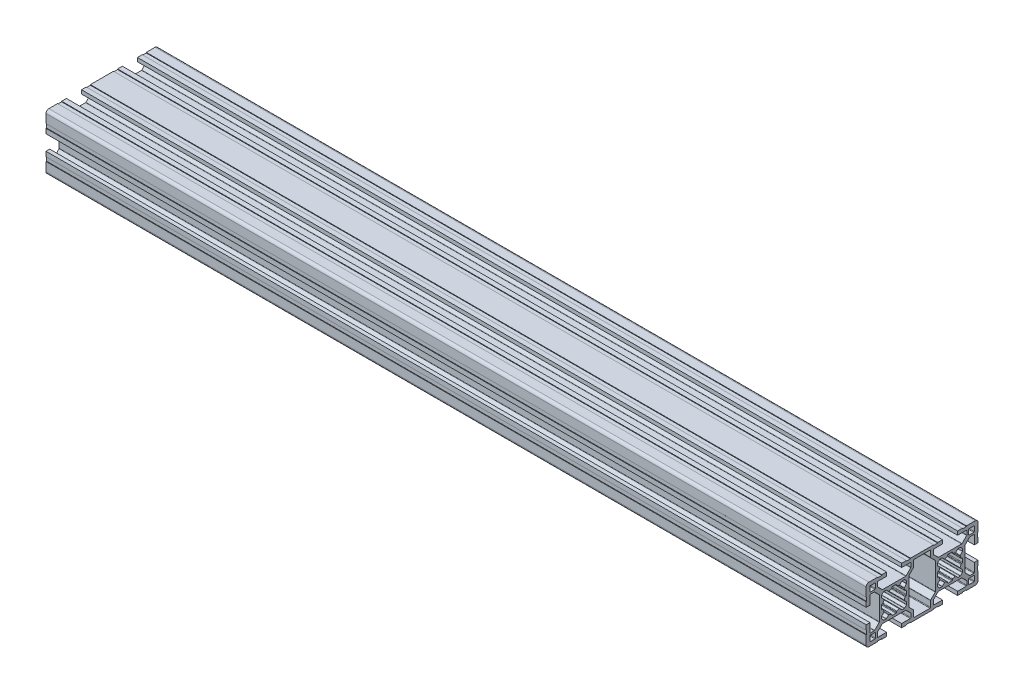
SolidWorks part; units mm, degrees
material "6063-T5 (Padrão)"
ref_plane "Plano frontal" through (0, 0, 0) normal (0, 0, 1) x (1, 0, 0)
ref_plane "Plano superior" through (0, 0, 0) normal (0, 1, 0) x (1, 0, 0)
ref_plane "Plano direito" through (0, 0, 0) normal (1, 0, 0) x (0, 0, -1)
sketch "Esboço1" plane through (0, 0, 0) normal (0, 0, 1) x (1, 0, 0)
  line L0 (-220, 0) -> (220, 0)
  point P4 (0, 0)
  dimension "D1" = 440
other "Retangular PF30-02 - PERFIL 3060 BÁSICO(1)"
ref_plane "Plano1" through (-220, 0, 0) normal (1, 0, 0) x (0, 1, 0)
sketch "Sketch11" plane through (-220, 0, 0) normal (1, 0, 0) x (0, 1, 0)
  line L0 (-9.8464, -4.5906) -> (-7.4222, -7.0149)
  line L1 (-7.21, -7.1028) -> (7.21, -7.1028)
  line L2 (7.4222, -7.0149) -> (9.8464, -4.5906)
  line L3 (10.0586, -4.5028) -> (13.2, -4.5028)
  line L4 (13.5, -4.2028) -> (13.5, 4.1972)
  line L5 (13.2, 4.4972) -> (10.0586, 4.4972)
  line L6 (9.8464, 4.5851) -> (7.4222, 7.0094)
  line L7 (7.21, 7.0972) -> (-7.21, 7.0972)
  line L8 (-7.4222, 7.0094) -> (-9.8464, 4.5851)
  line L9 (-10.0586, 4.4972) -> (-13.2, 4.4972)
  line L10 (-13.5, 4.1972) -> (-13.5, -4.2028)
  line L11 (-13.2, -4.5028) -> (-10.0586, -4.5028)
  line L12 (-6.7, 15.9528) -> (-6.7, 14.0528)
  line L13 (-6.1579, 16.2528) -> (-6.4, 16.2528)
  line L14 (-6.6121, 19.14) -> (-5.4871, 18.015)
  line L15 (-6.7, 20.4423) -> (-6.7, 19.3522)
  line L16 (-6.1319, 21.1347) -> (-6.6121, 20.6545)
  line L17 (-10.4678, 23.9149) -> (-7.9879, 21.435)
  line L18 (-12.7, 24.0028) -> (-10.6799, 24.0028)
  line L19 (-13, 19.0528) -> (-13, 23.7028)
  line L20 (-13, 19.0528) -> (-15, 19.0528)
  line L21 (6.7, 15.9528) -> (6.7, 14.0528)
  line L22 (7.9, 21.2229) -> (7.9, 8.7827)
  line L23 (15, 21.6028) -> (15, 19.0528)
  line L24 (-5.4396, 21.7028) -> (-4.3494, 21.7028)
  line L25 (-13, 25.3028) -> (-13, 27.7028)
  line L26 (-4.05, 28.0028) -> (-8.7, 28.0028)
  line L27 (-12.7, 28.0028) -> (-10.3, 28.0028)
  line L28 (-9, 27.7028) -> (-9, 25.6827)
  line L29 (-10, 27.7028) -> (-10, 25.3028)
  line L30 (-8.9121, 25.4705) -> (-6.4322, 22.9906)
  line L31 (15, 23.8028) -> (14.7, 23.8028)
  line L32 (14.7, 23.8028) -> (14.7, 21.6028)
  line L33 (15, 28.5028) -> (15, 23.8028)
  line L34 (8.8, 30.0028) -> (13.5, 30.0028)
  line L35 (8.8, 29.7028) -> (6.6, 29.7028)
  line L36 (4.05, 30.0028) -> (6.6, 30.0028)
  line L37 (4.05, 28.0028) -> (4.05, 30.0028)
  line L38 (10.3, 25.0028) -> (12.7, 25.0028)
  line L39 (15, 21.6028) -> (14.7, 21.6028)
  line L40 (6.6, 30.0028) -> (6.6, 29.7028)
  line L41 (-6.1319, 21.1347) -> (-5.6517, 21.6149)
  line L42 (-4.1373, 21.6149) -> (-3.0123, 20.4899)
  line L43 (-1.25, 21.1607) -> (-1.25, 21.4028)
  line L44 (8.8, 30.0028) -> (8.8, 29.7028)
  line L45 (1.25, 21.1607) -> (1.25, 21.4028)
  line L46 (4.1373, 21.6149) -> (3.0123, 20.4899)
  line L47 (6.1319, 21.1347) -> (5.6517, 21.6149)
  line L48 (8.9121, 25.4705) -> (6.4322, 22.9906)
  line L49 (10, 27.7028) -> (10, 25.3028)
  line L50 (9, 27.7028) -> (9, 25.6827)
  line L51 (12.7, 28.0028) -> (10.3, 28.0028)
  line L52 (4.05, 28.0028) -> (8.7, 28.0028)
  line L53 (13, 25.3028) -> (13, 27.7028)
  line L54 (5.4396, 21.7028) -> (4.3494, 21.7028)
  line L55 (13, 19.0528) -> (15, 19.0528)
  line L56 (13, 19.0528) -> (13, 23.7028)
  line L57 (12.7, 24.0028) -> (10.6799, 24.0028)
  line L58 (10.4678, 23.9149) -> (7.9879, 21.435)
  line L59 (6.1319, 21.1347) -> (6.6121, 20.6545)
  line L60 (6.7, 20.4423) -> (6.7, 19.3522)
  line L61 (6.6121, 19.14) -> (5.4871, 18.015)
  line L62 (6.1579, 16.2528) -> (6.4, 16.2528)
  line L63 (-7.9, 8.7827) -> (-7.9, 21.2229)
  line L64 (-0.95, 8.3028) -> (0.95, 8.3028)
  line L65 (-15, 8.4028) -> (-15, 10.9528)
  line L66 (-15, 6.2028) -> (-14.7, 6.2028)
  line L67 (-14.7, 6.2028) -> (-14.7, 8.4028)
  line L68 (-15, -14.9972) -> (15, -14.9972) construction
  line L69 (-6.1579, -13.7472) -> (-6.4, -13.7472)
  line L70 (-6.6121, -10.86) -> (-5.4871, -11.985)
  line L71 (-6.7, -9.5577) -> (-6.7, -10.6478)
  line L72 (-15, 8.4028) -> (-14.7, 8.4028)
  line L73 (-0.95, -21.6972) -> (0.95, -21.6972)
  line L74 (-6.1319, -8.8653) -> (-6.6121, -9.3455)
  line L75 (6.1579, 13.7528) -> (6.4, 13.7528)
  line L76 (6.6121, 10.8655) -> (5.4871, 11.9905)
  line L77 (6.7, 9.5632) -> (6.7, 10.6534)
  line L78 (6.1319, 8.8709) -> (6.6121, 9.3511)
  line L79 (10.4678, 6.0906) -> (7.9879, 8.5705)
  line L80 (12.7, 6.0028) -> (10.6799, 6.0028)
  line L81 (13, 10.9528) -> (13, 6.3028)
  line L82 (13, 10.9528) -> (15, 10.9528)
  line L83 (5.4396, 8.3028) -> (4.3494, 8.3028)
  line L84 (-10.4678, -6.0851) -> (-7.9879, -8.565)
  line L85 (-8.8, 30.0028) -> (-8.8, 29.7028)
  line L86 (-12.7, -5.9972) -> (-10.6799, -5.9972)
  line L87 (-13, -10.9472) -> (-13, -6.2972)
  line L88 (-13, -10.9472) -> (-15, -10.9472)
  line L89 (15, -8.3972) -> (15, -10.9472)
  line L90 (-5.4396, -8.2972) -> (-4.3494, -8.2972)
  line L91 (6.1319, 8.8709) -> (5.6517, 8.3906)
  line L92 (4.1373, 8.3906) -> (3.0123, 9.5156)
  line L93 (1.25, 8.8448) -> (1.25, 8.6028)
  line L94 (-15, -21.5972) -> (-15, -19.0472)
  line L95 (-6.6, 30.0028) -> (-6.6, 29.7028)
  line L96 (-1.25, 8.8448) -> (-1.25, 8.6028)
  line L97 (-4.1373, 8.3906) -> (-3.0123, 9.5156)
  line L98 (-6.1319, 8.8709) -> (-5.6517, 8.3906)
  line L99 (-15, -23.7972) -> (-14.7, -23.7972)
  line L100 (15, 8.4028) -> (14.7, 8.4028)
  line L101 (-14.7, -23.7972) -> (-14.7, -21.5972)
  line L102 (-15, -28.4972) -> (-15, -23.7972)
  line L103 (-8.8, -29.9972) -> (-13.5, -29.9972)
  line L104 (-8.8, -29.6972) -> (-6.6, -29.6972)
  line L105 (-4.05, -29.9972) -> (-6.6, -29.9972)
  line L106 (14.7, 6.2028) -> (14.7, 8.4028)
  line L107 (15, 6.2028) -> (14.7, 6.2028)
  line L108 (-4.05, -27.9972) -> (-4.05, -29.9972)
  line L109 (-10.3, -24.9972) -> (-12.7, -24.9972)
  line L110 (-6.2201, -22.8972) -> (6.2201, -22.8972)
  line L111 (-15, -21.5972) -> (-14.7, -21.5972)
  line L112 (15, -6.1972) -> (14.7, -6.1972)
  line L113 (-15, 21.6028) -> (-14.7, 21.6028)
  line L114 (-6.2201, 22.9028) -> (6.2201, 22.9028)
  line L115 (-10.3, 25.0028) -> (-12.7, 25.0028)
  line L116 (-4.05, 28.0028) -> (-4.05, 30.0028)
  line L117 (-4.05, 30.0028) -> (-6.6, 30.0028)
  line L118 (-8.8, 29.7028) -> (-6.6, 29.7028)
  line L119 (0, 29.9972) -> (0, -29.9972) construction
  line L120 (-15, 15.0028) -> (15, 15.0028) construction
  line L121 (-8.8, 30.0028) -> (-13.5, 30.0028)
  line L122 (-15, 28.5028) -> (-15, 23.8028)
  line L123 (-14.7, 23.8028) -> (-14.7, 21.6028)
  line L124 (-15, 23.8028) -> (-14.7, 23.8028)
  line L125 (-15, 21.6028) -> (-15, 19.0528)
  line L126 (14.7, -6.1972) -> (14.7, -8.3972)
  line L127 (-5.4396, 8.3028) -> (-4.3494, 8.3028)
  line L128 (15, 8.4028) -> (15, 10.9528)
  line L129 (15, 6.2028) -> (15, -6.1972)
  line L130 (-13, 10.9528) -> (-15, 10.9528)
  line L131 (-13, 10.9528) -> (-13, 6.3028)
  line L132 (-12.7, 6.0028) -> (-10.6799, 6.0028)
  line L133 (-10.4678, 6.0906) -> (-7.9879, 8.5705)
  line L134 (-6.1319, 8.8709) -> (-6.6121, 9.3511)
  line L135 (-0.95, 21.7028) -> (0.95, 21.7028)
  line L136 (-6.7, 9.5632) -> (-6.7, 10.6534)
  line L137 (-6.6121, 10.8655) -> (-5.4871, 11.9905)
  line L138 (-6.1579, 13.7528) -> (-6.4, 13.7528)
  line L139 (15, 0.0028) -> (-15, 0.0028) construction
  line L140 (15, -8.3972) -> (14.7, -8.3972)
  line L141 (-6.1319, -8.8653) -> (-5.6517, -8.3851)
  line L142 (-4.1373, -8.3851) -> (-3.0123, -9.5101)
  line L143 (-1.25, -8.8393) -> (-1.25, -8.5972)
  line L144 (-6.6, -29.9972) -> (-6.6, -29.6972)
  line L145 (1.25, -8.8393) -> (1.25, -8.5972)
  line L146 (4.1373, -8.3851) -> (3.0123, -9.5101)
  line L147 (6.1319, -8.8653) -> (5.6517, -8.3851)
  line L148 (-8.8, -29.9972) -> (-8.8, -29.6972)
  line L149 (5.4396, -8.2972) -> (4.3494, -8.2972)
  line L150 (13, -10.9472) -> (15, -10.9472)
  line L151 (13, -10.9472) -> (13, -6.2972)
  line L152 (12.7, -5.9972) -> (10.6799, -5.9972)
  line L153 (10.4678, -6.0851) -> (7.9879, -8.565)
  line L154 (6.1319, -8.8653) -> (6.6121, -9.3455)
  line L155 (6.7, -9.5577) -> (6.7, -10.6478)
  line L156 (6.6121, -10.86) -> (5.4871, -11.985)
  line L157 (6.1579, -13.7472) -> (6.4, -13.7472)
  line L158 (-15, -8.3972) -> (-14.7, -8.3972)
  line L159 (-15, 6.2028) -> (-15, -6.1972)
  line L160 (-14.7, -6.1972) -> (-14.7, -8.3972)
  line L161 (-15, -6.1972) -> (-14.7, -6.1972)
  line L162 (-15, -8.3972) -> (-15, -10.9472)
  line L163 (-0.95, -8.2972) -> (0.95, -8.2972)
  line L164 (-7.9, -8.7771) -> (-7.9, -21.2173)
  line L165 (6.1579, -16.2472) -> (6.4, -16.2472)
  line L166 (6.6121, -19.1345) -> (5.4871, -18.0095)
  line L167 (6.7, -20.4368) -> (6.7, -19.3466)
  line L168 (6.1319, -21.1291) -> (6.6121, -20.6489)
  line L169 (10.4678, -23.9094) -> (7.9879, -21.4295)
  line L170 (12.7, -23.9972) -> (10.6799, -23.9972)
  line L171 (13, -19.0472) -> (13, -23.6972)
  line L172 (13, -19.0472) -> (15, -19.0472)
  line L173 (5.4396, -21.6972) -> (4.3494, -21.6972)
  line L174 (13, -25.2972) -> (13, -27.6972)
  line L175 (4.05, -27.9972) -> (8.7, -27.9972)
  line L176 (12.7, -27.9972) -> (10.3, -27.9972)
  line L177 (9, -27.6972) -> (9, -25.6771)
  line L178 (10, -27.6972) -> (10, -25.2972)
  line L179 (8.9121, -25.465) -> (6.4322, -22.9851)
  line L180 (6.1319, -21.1291) -> (5.6517, -21.6093)
  line L181 (4.1373, -21.6093) -> (3.0123, -20.4844)
  line L182 (1.25, -21.1551) -> (1.25, -21.3972)
  line L183 (8.8, -29.9972) -> (8.8, -29.6972)
  line L184 (-1.25, -21.1551) -> (-1.25, -21.3972)
  line L185 (-4.1373, -21.6093) -> (-3.0123, -20.4844)
  line L186 (-6.1319, -21.1291) -> (-5.6517, -21.6093)
  line L187 (6.6, -29.9972) -> (6.6, -29.6972)
  line L188 (15, -21.5972) -> (14.7, -21.5972)
  line L189 (10.3, -24.9972) -> (12.7, -24.9972)
  line L190 (4.05, -27.9972) -> (4.05, -29.9972)
  line L191 (4.05, -29.9972) -> (6.6, -29.9972)
  line L192 (8.8, -29.6972) -> (6.6, -29.6972)
  line L193 (8.8, -29.9972) -> (13.5, -29.9972)
  line L194 (15, -28.4972) -> (15, -23.7972)
  line L195 (14.7, -23.7972) -> (14.7, -21.5972)
  line L196 (15, -23.7972) -> (14.7, -23.7972)
  line L197 (-8.9121, -25.465) -> (-6.4322, -22.9851)
  line L198 (-10, -27.6972) -> (-10, -25.2972)
  line L199 (-9, -27.6972) -> (-9, -25.6771)
  line L200 (-12.7, -27.9972) -> (-10.3, -27.9972)
  line L201 (-4.05, -27.9972) -> (-8.7, -27.9972)
  line L202 (-13, -25.2972) -> (-13, -27.6972)
  line L203 (-5.4396, -21.6972) -> (-4.3494, -21.6972)
  line L204 (15, -21.5972) -> (15, -19.0472)
  line L205 (7.9, -21.2173) -> (7.9, -8.7771)
  line L206 (6.7, -15.9472) -> (6.7, -14.0472)
  line L207 (-13, -19.0472) -> (-15, -19.0472)
  line L208 (-13, -19.0472) -> (-13, -23.6972)
  line L209 (-12.7, -23.9972) -> (-10.6799, -23.9972)
  line L210 (-10.4678, -23.9094) -> (-7.9879, -21.4295)
  line L211 (-6.1319, -21.1291) -> (-6.6121, -20.6489)
  line L212 (-6.7, -20.4368) -> (-6.7, -19.3466)
  line L213 (-6.6121, -19.1345) -> (-5.4871, -18.0095)
  line L214 (-6.1579, -16.2472) -> (-6.4, -16.2472)
  line L215 (-6.7, -15.9472) -> (-6.7, -14.0472)
  arc A0 (-9.8464, -4.5906) -> (-10.0586, -4.5028) centre (-10.0586, -4.8028) ccw
  arc A1 (-7.4222, -7.0149) -> (-7.21, -7.1028) centre (-7.21, -6.8028) ccw
  arc A2 (7.21, -7.1028) -> (7.4222, -7.0149) centre (7.21, -6.8028) ccw
  arc A3 (10.0586, -4.5028) -> (9.8464, -4.5906) centre (10.0586, -4.8028) ccw
  arc A4 (13.2, -4.5028) -> (13.5, -4.2028) centre (13.2, -4.2028) ccw
  arc A5 (13.5, 4.1972) -> (13.2, 4.4972) centre (13.2, 4.1972) ccw
  arc A6 (9.8464, 4.5851) -> (10.0586, 4.4972) centre (10.0586, 4.7972) ccw
  arc A7 (7.4222, 7.0094) -> (7.21, 7.0972) centre (7.21, 6.7972) ccw
  arc A8 (-7.21, 7.0972) -> (-7.4222, 7.0094) centre (-7.21, 6.7972) ccw
  arc A9 (-10.0586, 4.4972) -> (-9.8464, 4.5851) centre (-10.0586, 4.7972) ccw
  arc A10 (-13.2, 4.4972) -> (-13.5, 4.1972) centre (-13.2, 4.1972) ccw
  arc A11 (-13.5, -4.2028) -> (-13.2, -4.5028) centre (-13.2, -4.2028) ccw
  arc A12 (-6.4, 16.2528) -> (-6.7, 15.9528) centre (-6.4, 15.9528) ccw
  arc A13 (-5.867, 16.4795) -> (-6.1579, 16.2528) centre (-6.1579, 16.5528) cw
  arc A14 (-5.867, 16.4795) -> (-5.43, 17.6706) centre (0, 15.0028) cw
  arc A15 (-5.4871, 18.015) -> (-5.43, 17.6706) centre (-5.6993, 17.8029) cw
  arc A16 (-6.6121, 19.14) -> (-6.7, 19.3522) centre (-6.4, 19.3522) cw
  arc A17 (-6.6121, 20.6545) -> (-6.7, 20.4423) centre (-6.4, 20.4423) ccw
  arc A18 (-7.9879, 21.435) -> (-7.9, 21.2229) centre (-8.2, 21.2229) cw
  arc A19 (-10.6799, 24.0028) -> (-10.4678, 23.9149) centre (-10.6799, 23.7028) cw
  arc A20 (-13, 23.7028) -> (-12.7, 24.0028) centre (-12.7, 23.7028) cw
  arc A21 (13.5, 30.0028) -> (15, 28.5028) centre (13.5, 28.5028) cw
  arc A22 (1.25, 21.4028) -> (0.95, 21.7028) centre (0.95, 21.4028) ccw
  arc A23 (4.1373, 21.6149) -> (4.3494, 21.7028) centre (4.3494, 21.4028) cw
  arc A24 (1.4768, 20.8698) -> (1.25, 21.1607) centre (1.55, 21.1607) cw
  arc A25 (1.4768, 20.8698) -> (2.6678, 20.4328) centre (0, 15.0028) cw
  arc A26 (-10.3, 25.0028) -> (-10, 25.3028) centre (-10.3, 25.3028) ccw
  arc A27 (-6.4322, 22.9906) -> (-6.2201, 22.9028) centre (-6.2201, 23.2028) ccw
  arc A28 (-13, 25.3028) -> (-12.7, 25.0028) centre (-12.7, 25.3028) ccw
  arc A29 (-9, 25.6827) -> (-8.9121, 25.4705) centre (-8.7, 25.6827) ccw
  arc A30 (-10, 27.7028) -> (-10.3, 28.0028) centre (-10.3, 27.7028) ccw
  arc A31 (-8.7, 28.0028) -> (-9, 27.7028) centre (-8.7, 27.7028) ccw
  arc A32 (-12.7, 28.0028) -> (-13, 27.7028) centre (-12.7, 27.7028) ccw
  arc A33 (3.0123, 20.4899) -> (2.6678, 20.4328) centre (2.8001, 20.702) cw
  arc A34 (5.6517, 21.6149) -> (5.4396, 21.7028) centre (5.4396, 21.4028) ccw
  arc A35 (12.7, 28.0028) -> (13, 27.7028) centre (12.7, 27.7028) cw
  arc A36 (8.7, 28.0028) -> (9, 27.7028) centre (8.7, 27.7028) cw
  arc A37 (10, 27.7028) -> (10.3, 28.0028) centre (10.3, 27.7028) cw
  arc A38 (9, 25.6827) -> (8.9121, 25.4705) centre (8.7, 25.6827) cw
  arc A39 (13, 25.3028) -> (12.7, 25.0028) centre (12.7, 25.3028) cw
  arc A40 (6.4322, 22.9906) -> (6.2201, 22.9028) centre (6.2201, 23.2028) cw
  arc A41 (10.3, 25.0028) -> (10, 25.3028) centre (10.3, 25.3028) cw
  arc A42 (13, 23.7028) -> (12.7, 24.0028) centre (12.7, 23.7028) ccw
  arc A43 (10.6799, 24.0028) -> (10.4678, 23.9149) centre (10.6799, 23.7028) ccw
  arc A44 (7.9879, 21.435) -> (7.9, 21.2229) centre (8.2, 21.2229) ccw
  arc A45 (6.6121, 20.6545) -> (6.7, 20.4423) centre (6.4, 20.4423) cw
  arc A46 (6.6121, 19.14) -> (6.7, 19.3522) centre (6.4, 19.3522) ccw
  arc A47 (5.4871, 18.015) -> (5.43, 17.6706) centre (5.6993, 17.8029) ccw
  arc A48 (5.867, 16.4795) -> (5.43, 17.6706) centre (0, 15.0028) ccw
  arc A49 (5.867, 16.4795) -> (6.1579, 16.2528) centre (6.1579, 16.5528) ccw
  arc A50 (6.4, 16.2528) -> (6.7, 15.9528) centre (6.4, 15.9528) cw
  arc A51 (6.4, 13.7528) -> (6.7, 14.0528) centre (6.4, 14.0528) ccw
  arc A52 (-5.6517, 21.6149) -> (-5.4396, 21.7028) centre (-5.4396, 21.4028) cw
  arc A53 (-3.0123, 20.4899) -> (-2.6678, 20.4328) centre (-2.8001, 20.702) ccw
  arc A54 (-1.4768, 20.8698) -> (-2.6678, 20.4328) centre (0, 15.0028) ccw
  arc A55 (-1.4768, 20.8698) -> (-1.25, 21.1607) centre (-1.55, 21.1607) ccw
  arc A56 (-4.1373, 21.6149) -> (-4.3494, 21.7028) centre (-4.3494, 21.4028) ccw
  arc A57 (-6.4, 13.7528) -> (-6.7, 14.0528) centre (-6.4, 14.0528) cw
  arc A58 (-13.5, -29.9972) -> (-15, -28.4972) centre (-13.5, -28.4972) cw
  arc A59 (-1.25, 8.6028) -> (-0.95, 8.3028) centre (-0.95, 8.6028) ccw
  arc A60 (-4.1373, 8.3906) -> (-4.3494, 8.3028) centre (-4.3494, 8.6028) cw
  arc A61 (-1.4768, 9.1358) -> (-1.25, 8.8448) centre (-1.55, 8.8448) cw
  arc A62 (-1.4768, 9.1358) -> (-2.6678, 9.5728) centre (0, 15.0028) cw
  arc A63 (-3.0123, 9.5156) -> (-2.6678, 9.5728) centre (-2.8001, 9.3035) cw
  arc A64 (-5.6517, 8.3906) -> (-5.4396, 8.3028) centre (-5.4396, 8.6028) ccw
  arc A65 (5.867, 13.526) -> (6.1579, 13.7528) centre (6.1579, 13.4528) cw
  arc A66 (5.867, 13.526) -> (5.43, 12.3349) centre (0, 15.0028) cw
  arc A67 (5.4871, 11.9905) -> (5.43, 12.3349) centre (5.6993, 12.2026) cw
  arc A68 (6.6121, 10.8655) -> (6.7, 10.6534) centre (6.4, 10.6534) cw
  arc A69 (6.6121, 9.3511) -> (6.7, 9.5632) centre (6.4, 9.5632) ccw
  arc A70 (7.9879, 8.5705) -> (7.9, 8.7827) centre (8.2, 8.7827) cw
  arc A71 (10.6799, 6.0028) -> (10.4678, 6.0906) centre (10.6799, 6.3028) cw
  arc A72 (13, 6.3028) -> (12.7, 6.0028) centre (12.7, 6.3028) cw
  arc A73 (-5.867, -13.5205) -> (-6.1579, -13.7472) centre (-6.1579, -13.4472) cw
  arc A74 (-5.867, -13.5205) -> (-5.43, -12.3294) centre (0, -14.9972) cw
  arc A75 (-1.25, -21.3972) -> (-0.95, -21.6972) centre (-0.95, -21.3972) ccw
  arc A76 (-5.4871, -11.985) -> (-5.43, -12.3294) centre (-5.6993, -12.1971) cw
  arc A77 (-6.6121, -10.86) -> (-6.7, -10.6478) centre (-6.4, -10.6478) cw
  arc A78 (-6.6121, -9.3455) -> (-6.7, -9.5577) centre (-6.4, -9.5577) ccw
  arc A79 (-7.9879, -8.565) -> (-7.9, -8.7771) centre (-8.2, -8.7771) cw
  arc A80 (5.6517, 8.3906) -> (5.4396, 8.3028) centre (5.4396, 8.6028) cw
  arc A81 (3.0123, 9.5156) -> (2.6678, 9.5728) centre (2.8001, 9.3035) ccw
  arc A82 (-10.6799, -5.9972) -> (-10.4678, -6.0851) centre (-10.6799, -6.2972) cw
  arc A83 (-13, -6.2972) -> (-12.7, -5.9972) centre (-12.7, -6.2972) cw
  arc A84 (1.25, -8.5972) -> (0.95, -8.2972) centre (0.95, -8.5972) ccw
  arc A85 (4.1373, -8.3851) -> (4.3494, -8.2972) centre (4.3494, -8.5972) cw
  arc A86 (1.4768, -9.1302) -> (1.25, -8.8393) centre (1.55, -8.8393) cw
  arc A87 (1.4768, -9.1302) -> (2.6678, -9.5672) centre (0, -14.9972) cw
  arc A88 (3.0123, -9.5101) -> (2.6678, -9.5672) centre (2.8001, -9.2979) cw
  arc A89 (1.4768, 9.1358) -> (2.6678, 9.5728) centre (0, 15.0028) ccw
  arc A90 (1.4768, 9.1358) -> (1.25, 8.8448) centre (1.55, 8.8448) ccw
  arc A91 (4.1373, 8.3906) -> (4.3494, 8.3028) centre (4.3494, 8.6028) ccw
  arc A92 (1.25, 8.6028) -> (0.95, 8.3028) centre (0.95, 8.6028) cw
  arc A93 (5.6517, -8.3851) -> (5.4396, -8.2972) centre (5.4396, -8.5972) ccw
  arc A94 (-13, 6.3028) -> (-12.7, 6.0028) centre (-12.7, 6.3028) ccw
  arc A95 (-10.6799, 6.0028) -> (-10.4678, 6.0906) centre (-10.6799, 6.3028) ccw
  arc A96 (-7.9879, 8.5705) -> (-7.9, 8.7827) centre (-8.2, 8.7827) ccw
  arc A97 (-6.6121, 9.3511) -> (-6.7, 9.5632) centre (-6.4, 9.5632) cw
  arc A98 (-6.6121, 10.8655) -> (-6.7, 10.6534) centre (-6.4, 10.6534) ccw
  arc A99 (-5.4871, 11.9905) -> (-5.43, 12.3349) centre (-5.6993, 12.2026) ccw
  arc A100 (-1.25, 21.4028) -> (-0.95, 21.7028) centre (-0.95, 21.4028) cw
  arc A101 (-5.867, 13.526) -> (-5.43, 12.3349) centre (0, 15.0028) ccw
  arc A102 (-5.867, 13.526) -> (-6.1579, 13.7528) centre (-6.1579, 13.4528) ccw
  arc A103 (-13.5, 30.0028) -> (-15, 28.5028) centre (-13.5, 28.5028) ccw
  arc A104 (13, -6.2972) -> (12.7, -5.9972) centre (12.7, -6.2972) ccw
  arc A105 (10.6799, -5.9972) -> (10.4678, -6.0851) centre (10.6799, -6.2972) ccw
  arc A106 (7.9879, -8.565) -> (7.9, -8.7771) centre (8.2, -8.7771) ccw
  arc A107 (6.6121, -9.3455) -> (6.7, -9.5577) centre (6.4, -9.5577) cw
  arc A108 (6.6121, -10.86) -> (6.7, -10.6478) centre (6.4, -10.6478) ccw
  arc A109 (5.4871, -11.985) -> (5.43, -12.3294) centre (5.6993, -12.1971) ccw
  arc A110 (5.867, -13.5205) -> (5.43, -12.3294) centre (0, -14.9972) ccw
  arc A111 (5.867, -13.5205) -> (6.1579, -13.7472) centre (6.1579, -13.4472) ccw
  arc A112 (-5.6517, -8.3851) -> (-5.4396, -8.2972) centre (-5.4396, -8.5972) cw
  arc A113 (-3.0123, -9.5101) -> (-2.6678, -9.5672) centre (-2.8001, -9.2979) ccw
  arc A114 (-1.4768, -9.1302) -> (-2.6678, -9.5672) centre (0, -14.9972) ccw
  arc A115 (-1.4768, -9.1302) -> (-1.25, -8.8393) centre (-1.55, -8.8393) ccw
  arc A116 (-4.1373, -8.3851) -> (-4.3494, -8.2972) centre (-4.3494, -8.5972) ccw
  arc A117 (-1.25, -8.5972) -> (-0.95, -8.2972) centre (-0.95, -8.5972) cw
  arc A118 (-6.4, -13.7472) -> (-6.7, -14.0472) centre (-6.4, -14.0472) ccw
  arc A119 (-4.1373, -21.6093) -> (-4.3494, -21.6972) centre (-4.3494, -21.3972) cw
  arc A120 (-1.4768, -20.8642) -> (-1.25, -21.1551) centre (-1.55, -21.1551) cw
  arc A121 (-1.4768, -20.8642) -> (-2.6678, -20.4272) centre (0, -14.9972) cw
  arc A122 (-3.0123, -20.4844) -> (-2.6678, -20.4272) centre (-2.8001, -20.6965) cw
  arc A123 (-5.6517, -21.6093) -> (-5.4396, -21.6972) centre (-5.4396, -21.3972) ccw
  arc A124 (6.4, -13.7472) -> (6.7, -14.0472) centre (6.4, -14.0472) cw
  arc A125 (6.4, -16.2472) -> (6.7, -15.9472) centre (6.4, -15.9472) ccw
  arc A126 (5.867, -16.474) -> (6.1579, -16.2472) centre (6.1579, -16.5472) cw
  arc A127 (5.867, -16.474) -> (5.43, -17.6651) centre (0, -14.9972) cw
  arc A128 (5.4871, -18.0095) -> (5.43, -17.6651) centre (5.6993, -17.7974) cw
  arc A129 (6.6121, -19.1345) -> (6.7, -19.3466) centre (6.4, -19.3466) cw
  arc A130 (6.6121, -20.6489) -> (6.7, -20.4368) centre (6.4, -20.4368) ccw
  arc A131 (7.9879, -21.4295) -> (7.9, -21.2173) centre (8.2, -21.2173) cw
  arc A132 (10.6799, -23.9972) -> (10.4678, -23.9094) centre (10.6799, -23.6972) cw
  arc A133 (13, -23.6972) -> (12.7, -23.9972) centre (12.7, -23.6972) cw
  arc A134 (10.3, -24.9972) -> (10, -25.2972) centre (10.3, -25.2972) ccw
  arc A135 (6.4322, -22.9851) -> (6.2201, -22.8972) centre (6.2201, -23.1972) ccw
  arc A136 (13, -25.2972) -> (12.7, -24.9972) centre (12.7, -25.2972) ccw
  arc A137 (9, -25.6771) -> (8.9121, -25.465) centre (8.7, -25.6771) ccw
  arc A138 (10, -27.6972) -> (10.3, -27.9972) centre (10.3, -27.6972) ccw
  arc A139 (8.7, -27.9972) -> (9, -27.6972) centre (8.7, -27.6972) ccw
  arc A140 (12.7, -27.9972) -> (13, -27.6972) centre (12.7, -27.6972) ccw
  arc A141 (5.6517, -21.6093) -> (5.4396, -21.6972) centre (5.4396, -21.3972) cw
  arc A142 (3.0123, -20.4844) -> (2.6678, -20.4272) centre (2.8001, -20.6965) ccw
  arc A143 (-12.7, -27.9972) -> (-13, -27.6972) centre (-12.7, -27.6972) cw
  arc A144 (-8.7, -27.9972) -> (-9, -27.6972) centre (-8.7, -27.6972) cw
  arc A145 (-10, -27.6972) -> (-10.3, -27.9972) centre (-10.3, -27.6972) cw
  arc A146 (-9, -25.6771) -> (-8.9121, -25.465) centre (-8.7, -25.6771) cw
  arc A147 (-13, -25.2972) -> (-12.7, -24.9972) centre (-12.7, -25.2972) cw
  arc A148 (-6.4322, -22.9851) -> (-6.2201, -22.8972) centre (-6.2201, -23.1972) cw
  arc A149 (-10.3, -24.9972) -> (-10, -25.2972) centre (-10.3, -25.2972) cw
  arc A150 (1.4768, -20.8642) -> (2.6678, -20.4272) centre (0, -14.9972) ccw
  arc A151 (1.4768, -20.8642) -> (1.25, -21.1551) centre (1.55, -21.1551) ccw
  arc A152 (4.1373, -21.6093) -> (4.3494, -21.6972) centre (4.3494, -21.3972) ccw
  arc A153 (1.25, -21.3972) -> (0.95, -21.6972) centre (0.95, -21.3972) cw
  arc A154 (13.5, -29.9972) -> (15, -28.4972) centre (13.5, -28.4972) ccw
  arc A155 (-13, -23.6972) -> (-12.7, -23.9972) centre (-12.7, -23.6972) ccw
  arc A156 (-10.6799, -23.9972) -> (-10.4678, -23.9094) centre (-10.6799, -23.6972) ccw
  arc A157 (-7.9879, -21.4295) -> (-7.9, -21.2173) centre (-8.2, -21.2173) ccw
  arc A158 (-6.6121, -20.6489) -> (-6.7, -20.4368) centre (-6.4, -20.4368) cw
  arc A159 (-6.6121, -19.1345) -> (-6.7, -19.3466) centre (-6.4, -19.3466) ccw
  arc A160 (-5.4871, -18.0095) -> (-5.43, -17.6651) centre (-5.6993, -17.7974) ccw
  arc A161 (-5.867, -16.474) -> (-5.43, -17.6651) centre (0, -14.9972) ccw
  arc A162 (-5.867, -16.474) -> (-6.1579, -16.2472) centre (-6.1579, -16.5472) ccw
  arc A163 (-6.4, -16.2472) -> (-6.7, -15.9472) centre (-6.4, -15.9472) cw
  point P36 (-15, -14.9972)
  point P37 (0, 15.0028)
  point P66 (-11.6899, 24.0028)
  point P156 (0, 30.0028)
  point P176 (15, 30.0028)
  point P177 (11.6899, 24.0028)
  point P179 (-6.7, 15.0028)
  point P180 (6.7, 15.0028)
  point P187 (0, -0.0028)
  point P291 (15, -14.9972)
  point P315 (0, 29.9972)
  point P317 (15, 15.0028)
  point P321 (-15, 15.0028)
  point P322 (-15, 30.0028)
  point P324 (0, 15.0028)
  point P357 (-15, 0.0028)
  point P358 (0, 0.0083)
  point P359 (11.6899, 6.0028)
  point P360 (15, 0.0028)
  point P361 (0, 0.0028)
  point P362 (-11.6899, 6.0028)
  point P534 (0, -14.9972)
  point P539 (-15, -29.9972)
  point P557 (-11.6899, -5.9972)
  point P558 (11.6899, -5.9972)
  point P559 (0, -29.9917)
  point P560 (6.7, -14.9972)
  point P561 (-6.7, -14.9972)
  point P562 (11.6899, -23.9972)
  point P563 (15, -29.9972)
  point P564 (0, -29.9972)
  point P565 (-11.6899, -23.9972)
  point P566 (0, 0)
